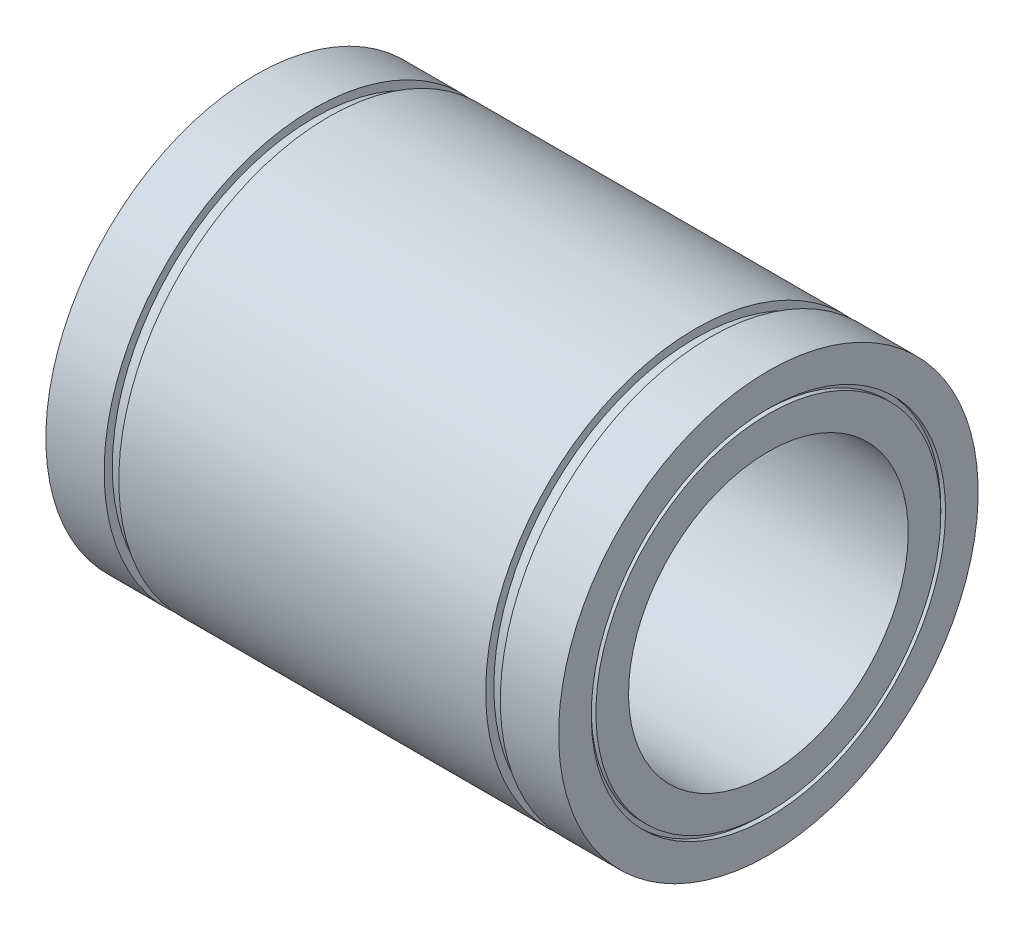
SolidWorks part; units mm, degrees
material "Ст3сп ГОСТ 535-2005"
ref_plane "Plano frontal" through (0, 0, 0) normal (0, 0, 1) x (1, 0, 0)
ref_plane "Plano superior" through (0, 0, 0) normal (0, 1, 0) x (1, 0, 0)
ref_plane "Plano direito" through (0, 0, 0) normal (1, 0, 0) x (0, 0, -1)
sketch "Esboço1" plane through (0, 0, 0) normal (0, 0, 1) x (1, 0, 0)
  line L0 (-55, 45) -> (-42.5, 45)
  line L1 (-42.5, 45) -> (-42.5, 43.25)
  line L2 (-42.5, 43.25) -> (-39.35, 43.25)
  line L3 (-39.35, 43.25) -> (-39.35, 45)
  line L4 (-39.35, 45) -> (39.35, 45)
  line L5 (39.35, 45) -> (39.35, 43.25)
  line L6 (39.35, 43.25) -> (42.5, 43.25)
  line L7 (42.5, 43.25) -> (42.5, 45)
  line L8 (42.5, 45) -> (55, 45)
  line L9 (55, 45) -> (55, 38)
  line L10 (55, 30) -> (-55, 30)
  line L11 (-55, 30) -> (-55, 37)
  line L12 (0, 30) -> (0, 0) construction
  line L13 (0, 0) -> (-86.5, 0) construction
  line L14 (-55, 38) -> (-55, 45)
  line L15 (-55, 38) -> (-54, 38)
  line L16 (55, 37) -> (55, 30)
  line L17 (-54, 38) -> (-54, 37)
  line L18 (-54, 37) -> (-55, 37)
  line L19 (55, 38) -> (54, 38)
  line L21 (55, 37) -> (54, 37)
  line L22 (54, 38) -> (54, 37)
  dimension "D1" = 110
  dimension "D2" = 85
  dimension "D3" = 3.15
  dimension "D4" = 60
  dimension "D5" = 90
  dimension "D6" = 86.5
  dimension "D7" = 1
  dimension "D8" = 1
  dimension "D9" = 1
  dimension "D10" = 1
revolve "Revolução1" add sketch "Esboço1" angle 360 about L13
